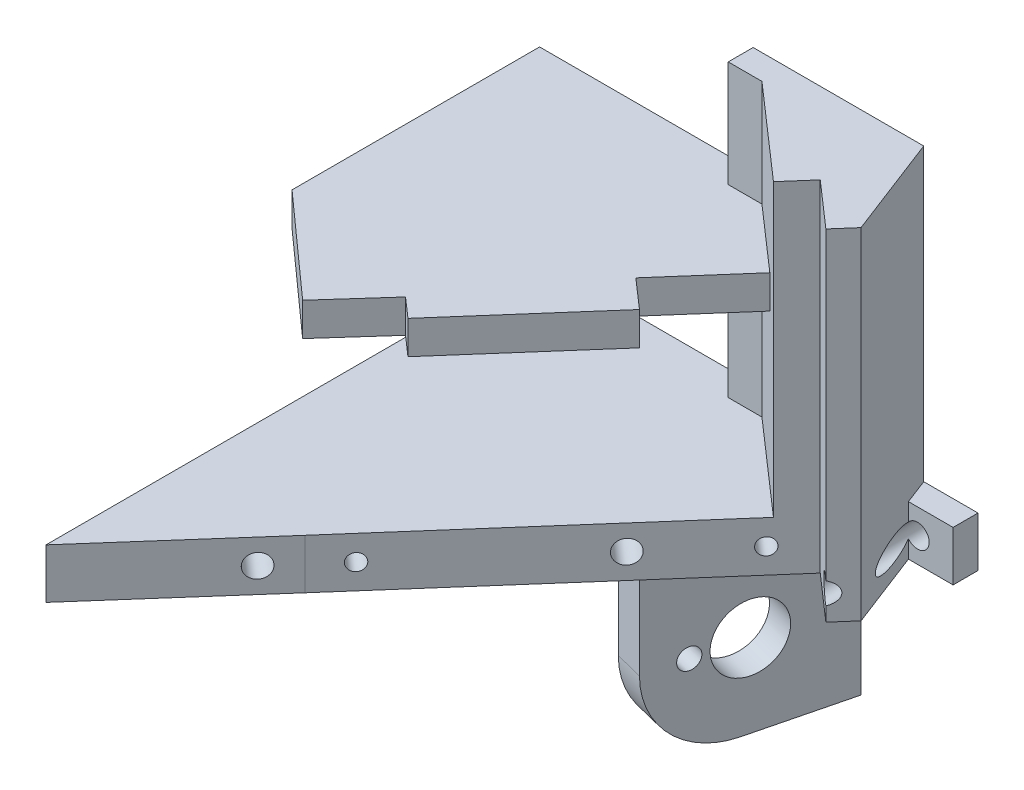
SolidWorks part; units mm, degrees
ref_plane "Plan de face" through (0, 0, 0) normal (0, 0, 1) x (1, 0, 0)
ref_plane "Plan de dessus" through (0, 0, 0) normal (0, 1, 0) x (1, 0, 0)
ref_plane "Plan de droite" through (0, 0, 0) normal (1, 0, 0) x (0, 0, -1)
sketch "Esquisse2" plane through (0, 0, 0) normal (0, 0, 1) x (1, 0, 0)
  line L0 (12, -24.85) -> (-7, -24.85) construction
  line L7 (10.2685, 5.15) -> (75.2685, 5.15) construction
  line L8 (10.2685, 5.15) -> (10.2685, -54.85) construction
  line L9 (10.2685, -54.85) -> (75.2685, -54.85) construction
  line L10 (75.2685, 5.15) -> (75.2685, -54.85) construction
  point P19 (2.5, -24.85)
  dimension "D2" = 65
sketch "Esquisse4" plane through (0, 0, 0) normal (0, 0, 1) x (1, 0, 0)
  line L0 (10.2685, -54.85) -> (75.2685, -54.85) construction
  line L1 (74.4742, -54.85) -> (21.6926, -54.85)
  line L2 (74.4742, -54.85) -> (74.4742, -48.85)
  line L3 (74.4742, -48.85) -> (21.6926, -48.85)
  line L4 (21.6926, -54.85) -> (21.6926, -48.85)
extrude "Boss.-Extru.1" add sketch "Esquisse4" along normal blind 3
sketch "Esquisse6" plane through (0, -54.85, 0) normal (0, -1, 0) x (1, 0, 0)
  line L0 (57.5204, 3) -> (76.1395, 19.3022) construction
  line L1 (65.2422, 9.761) -> (36.2711, 42.8496) construction
  line L2 (21.6926, 3) -> (74.4742, 3) construction
  line L3 (57.5204, 3) -> (21.6926, 3) construction
  line L4 (21.6926, 3) -> (21.6926, 29.8045) construction
  line L5 (21.6926, 29.8045) -> (36.2711, 42.8496) construction
  line L6 (65.2422, 9.761) -> (70.7001, 14.5397)
  line L7 (70.7001, 14.5397) -> (72.6763, 12.2826)
  line L8 (72.6763, 12.2826) -> (62.0745, 3)
  line L9 (65.2422, 9.761) -> (36.2711, 42.8496)
  line L11 (21.6926, 29.8045) -> (21.6926, 3)
  line L12 (21.6926, 3) -> (62.0745, 3)
  line L13 (21.6926, 59.4233) -> (21.6926, 29.8045)
  line L14 (21.6926, 59.4233) -> (36.2711, 42.8496)
extrude "Boss.-Extru.2" add sketch "Esquisse6" against normal blind 41
sketch "Esquisse9" plane through (0, -13.85, 0) normal (0, 1, 0) x (1, 0, 0)
  line L0 (65.2422, -9.761) -> (70.7001, -14.5397) construction
  line L1 (70.7001, -14.5397) -> (72.6763, -12.2826) construction
  line L2 (72.6763, -12.2826) -> (62.0745, -3) construction
  line L3 (62.0745, -3) -> (72.6763, -12.2826) construction
  line L4 (62.0745, -3) -> (21.6926, -3) construction
  line L5 (21.6926, -3) -> (21.6926, -29.8045) construction
  line L6 (21.6926, -29.8045) -> (36.2711, -42.8496) construction
  line L7 (36.2711, -42.8496) -> (65.2422, -9.761) construction
  line L8 (70.7001, -14.5397) -> (57.5204, -3) construction
  line L9 (62.6131, -12.7638) -> (51.4617, -3) construction
  line L10 (36.2711, -42.8496) -> (62.6131, -12.7638)
  line L11 (62.6131, -12.7638) -> (51.4617, -3)
  line L12 (51.4617, -3) -> (21.6926, -3)
  line L13 (21.6926, -3) -> (21.6926, -29.8045)
  line L15 (36.2711, -42.8496) -> (21.6926, -59.4233)
  line L16 (21.6926, -59.4233) -> (21.6926, -29.8045)
extrude "Enlèv. mat.-Extru.1" cut sketch "Esquisse9" against normal blind 35
ref_plane "Plan1" through (0, -26.6447, 0) normal (0, 1, 0) x (1, 0, 0)
sketch "Esquisse10" plane through (0, -26.6447, 0) normal (0, 1, 0) x (1, 0, 0)
  line L0 (21.6926, 0) -> (21.6926, -29.8045) construction
  line L1 (21.6926, -29.8045) -> (36.2711, -42.8496) construction
  line L2 (36.2711, -42.8496) -> (65.2422, -9.761) construction
  line L3 (65.2422, -9.761) -> (54.094, 0) construction
  line L4 (10.2685, 0) -> (75.2685, 0) construction
  line L5 (54.094, 0) -> (21.6926, 0) construction
  line L6 (62.6131, -12.7638) -> (48.0353, 0) construction
  line L7 (42.0722, -36.224) -> (39.691, -34.1392)
  line L8 (42.0722, -36.224) -> (55.082, -21.3652)
  line L9 (55.082, -21.3652) -> (51.5638, -18.2849)
  line L10 (51.5638, -18.2849) -> (59.0949, -9.6834)
  line L11 (59.0949, -9.6834) -> (48.0353, 0)
  line L12 (48.0353, 0) -> (21.6926, 0)
  line L13 (21.6926, 0) -> (21.6926, -29.8045)
  line L14 (39.691, -34.1392) -> (33.8419, -40.6759)
  line L15 (33.8419, -40.6759) -> (21.6926, -29.8045)
extrude "Boss.-Extru.3" add sketch "Esquisse10" against normal blind 4
sketch "Esquisse11" plane through (41.7684, 0, 36.5709) normal (0.7524, 0, 0.6587) x (0.6587, 0, -0.7524)
  line L0 (-30.4182, -51.85) -> (35.6341, -51.85) construction
  line L2 (35.6341, -13.85) -> (35.6341, -54.85) construction
  line L3 (-30.4182, -48.85) -> (-30.4182, -54.85) construction
  line L4 (-30.4182, -48.85) -> (-30.4182, -54.85) construction
  circle A0 centre (19.1341, -51.85) radius 1.4
  circle A1 centre (-12.3659, -51.85) radius 1.4
  dimension "D1" = 16.5
  dimension "D2" = 48
extrude "Enlèv. mat.-Extru.2" cut sketch "Esquisse11" against normal blind 43
sketch "Esquisse13" plane through (0, -54.85, 0) normal (0, -1, 0) x (1, 0, 0)
  line L0 (70.7001, 14.5397) -> (60.2134, 5.3579)
  line L2 (60.2134, 0) -> (67.9411, 0)
  line L3 (10.2685, 0) -> (75.2685, 0) construction
  line L4 (67.9411, 0) -> (72.6763, 12.2826)
  line L5 (72.6763, 12.2826) -> (70.7001, 14.5397)
  line L6 (60.2134, 5.3579) -> (60.2134, 0)
extrude "Boss.-Extru.4" add sketch "Esquisse13" against normal blind 41
sketch "Esquisse15" plane through (41.7684, 0, 36.5709) normal (0.7524, 0, 0.6587) x (0.6587, 0, -0.7524)
  line L0 (-8.3452, -51.85) -> (26.6548, -51.85) construction
  line L1 (-8.3452, -48.85) -> (-8.3452, -54.85) construction
  line L2 (13.5341, -30.6447) -> (13.5341, -57.0427) construction
  line L4 (35.6341, -54.85) -> (35.6341, -46.1248) construction
  line L5 (35.6341, -13.85) -> (35.6341, -54.85) construction
  circle A0 centre (31.0341, -51.85) radius 1
  circle A1 centre (-3.9659, -51.85) radius 1
  dimension "D1" = 4.6
  dimension "D2" = 17.5
extrude "Enlèv. mat.-Extru.4" cut sketch "Esquisse15" against normal blind 30
sketch "Esquisse16" plane through (0, -54.85, 0) normal (0, 1, 0) x (1, 0, 0)
  line L0 (60.4176, 0) -> (55.082, -21.3652)
  line L1 (10.2685, 0) -> (75.2685, 0) construction
  line L2 (55.082, -21.3652) -> (51.6863, -20.5172)
  line L3 (51.6863, -20.5172) -> (56.8101, 0)
  line L4 (56.8101, 0) -> (60.4176, 0)
  dimension "D1" = 3.5
extrude "Boss.-Extru.5" add sketch "Esquisse16" against normal blind 20
sketch "Esquisse18" plane through (56.8707, 0, 14.2026) normal (0.9702, 0, 0.2423) x (0.2423, 0, -0.9702)
  line L0 (-7.3826, -64.85) -> (14.6388, -64.85) construction
  line L1 (-7.3826, -74.85) -> (-7.3826, -54.85) construction
  line L2 (14.6388, -74.85) -> (14.6388, -54.85) construction
  circle A0 centre (3.6281, -64.85) radius 4
extrude "Enlèv. mat.-Extru.5" cut sketch "Esquisse18" against normal blind 12
sketch "Esquisse12" plane through (0, 0, 0) normal (0, 0, -1) x (-1, 0, 0)
  line L0 (-70.1979, -51.85) -> (-70.1979, 5.5425) construction
  line L1 (-21.6926, -48.85) -> (-21.6926, -54.85) construction
  line L7 (-23.3509, -54.4575) -> (-23.3509, 5.5425) construction
  line L8 (-70.1979, -51.85) -> (-21.6926, -51.85) construction
  circle B0 centre (-24.43, -51.85) radius 1.4
  circle B1 centre (-43.53, -51.85) radius 1.4
  circle B2 centre (-55.1979, -51.85) radius 1.4
  circle B3 centre (-70.1979, -51.85) radius 1.4
sketch_block_instance "Bloc1-1"
sketch_block "Bloc1" parameters "D1"=1.7
extrude "Enlèv. mat.-Extru.6" cut sketch "Esquisse12" against normal blind 18
sketch "Esquisse19" plane through (56.8707, 0, 14.2026) normal (0.9702, 0, 0.2423) x (0.2423, 0, -0.9702)
  line L0 (-0.3719, -64.85) -> (-7.3826, -64.85) construction
  line L1 (-7.3826, -74.85) -> (-7.3826, -54.85) construction
  circle A0 centre (3.6281, -64.85) radius 4 construction
  circle A1 centre (-2.4361, -64.85) radius 1.2546
extrude "Enlèv. mat.-Extru.7" cut sketch "Esquisse19" against normal blind 18
fillet "Congé1" radius 10 1 edges at (53.3841, -74.85, 20.9412)
sketch "Esquisse20" plane through (0, -13.85, 0) normal (0, 1, 0) x (1, 0, 0)
  line L1 (60.2134, -3) -> (47.4016, -3)
  line L2 (60.2134, -3) -> (60.2134, 0)
  line L3 (60.2134, 0) -> (47.4016, 0)
  line L4 (47.4016, -3) -> (47.4016, 0)
extrude "Boss.-Extru.7" add sketch "Esquisse20" against normal blind 36
